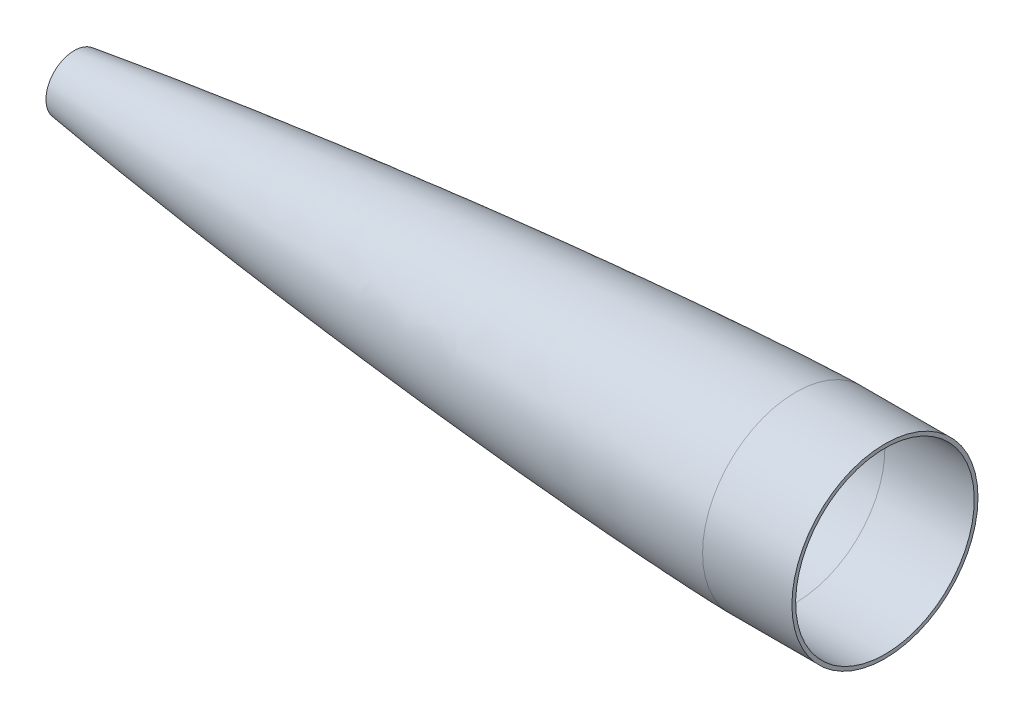
SolidWorks part; units mm, degrees
material "S-Glass Fiber"
ref_plane "Front Plane" through (0, 0, 0) normal (0, 0, 1) x (1, 0, 0)
ref_plane "Top Plane" through (0, 0, 0) normal (0, 1, 0) x (1, 0, 0)
ref_plane "Right Plane" through (0, 0, 0) normal (1, 0, 0) x (0, 0, -1)
sketch "Sketch2" plane through (0, 0, 0) normal (0, 0, 1) x (1, 0, 0)
  line L3 (762, 76.2) -> (762, 0) construction
  line L8 (762, 76.2) -> (762, 0) construction
  line L9 (146.6256, 0) -> (146.6256, 20.574) construction
  line L13 (0, 0) -> (762, 0) construction
  line L14 (0, 0) -> (2.6005, 0)
  line L15 (2.6005, 0) -> (146.6256, 20.574)
  line L16 (146.6256, 20.574) -> (146.6256, 24.13) construction
  line L18 (762, 79.375) -> (838.2, 79.375)
  line L19 (838.2, 79.375) -> (838.2, 76.2)
  line L20 (838.2, 76.2) -> (762, 76.2)
  line L21 (762, 79.375) -> (762, 76.2) construction
  spline S0 degree 4 poles (-49.3803, -13.3951) (-49.3774, -13.3872) (-49.3706, -13.3719) (-49.3515, -13.3442) (-49.3178, -13.3067) (-49.276, -13.2657) (-49.2126, -13.2108) (-49.1334, -13.1488) (-49.0162, -13.0653) (-48.8589, -12.9635) (-48.6742, -12.8535) (-48.4619, -12.7357) (-48.1531, -12.5738) (-47.6707, -12.3385) (-46.8508, -11.9725) (-45.384, -11.3821) (-42.7412, -10.4344) (-37.8908, -8.9033) (-28.7853, -6.3974) (-12.8846, -2.6091) (14.0481, 2.9702) (50.9813, 9.6302) (95.7045, 16.8265) (145.382, 24.0733) (195.1363, 30.7674) (244.9501, 37.002) (294.8122, 42.8365) (344.7156, 48.3061) (394.6553, 53.4327) (444.6281, 58.2264) (494.6316, 62.6884) (544.6644, 66.8095) (594.7257, 70.5693) (638.5543, 73.5096) (676.1401, 75.7375) (706.4525, 77.3031) (726.8599, 78.2225) (743.6263, 78.8648) (754.1247, 79.1902) (759.3746, 79.3253) (762, 79.375) knots 0 0 0 0 0 0.000041 0.000082 0.000164 0.000246 0.000328 0.000492 0.000655 0.000949 0.001243 0.001543 0.001842 0.002654 0.003867 0.005932 0.009572 0.01638 0.028732 0.052102 0.089485 0.150853 0.212221 0.27359 0.334958 0.396326 0.457695 0.519063 0.580431 0.6418 0.703168 0.764537 0.825905 0.887273 0.917957 0.948642 0.974321 0.98716 1 1 1 1 1 construction
  spline S1 degree 4 poles (0, 0) (5.3576, 1.0979) (23.0362, 4.5882) (53.13, 9.9759) (95.7045, 16.8265) (145.382, 24.0733) (195.1363, 30.7674) (244.9501, 37.002) (294.8122, 42.8365) (344.7156, 48.3061) (394.6553, 53.4327) (444.6281, 58.2264) (494.6316, 62.6884) (544.6644, 66.8095) (594.7257, 70.5693) (638.5543, 73.5096) (676.1401, 75.7375) (706.4525, 77.3031) (726.8599, 78.2225) (743.6263, 78.8648) (754.1247, 79.1902) (759.3746, 79.3253) (762, 79.375) knots 0.062743 0.062743 0.062743 0.062743 0.062743 0.089485 0.150853 0.212221 0.27359 0.334958 0.396326 0.457695 0.519063 0.580431 0.6418 0.703168 0.764537 0.825905 0.887273 0.917957 0.948642 0.974321 0.98716 1 1 1 1 1
  spline S2 degree 2 poles (146.6256, 20.574) (453.6076, 56.3921) (762, 76.2) knots 0 0 0 1 1 1
  point P1 (762, 92.8903)
  dimension "D1" = 24.13
  dimension "D2" = 146.6256
  dimension "D3" = 76.2
  dimension "D4" = 254
  dimension "D5" = 57.15
  dimension "D6" = 79.375
  dimension "32" = 762
  dimension "D7" = 20.574
  dimension "D8" = 2.6005
  dimension "D9" = 76.2
revolve "Revolve2" add sketch "Sketch2" angle 360 about L13
sketch "Sketch4" plane through (0, 0, 0) normal (1, 0, 0) x (0, 0, -1)
  circle A0 centre (0, 0) radius 24.13
  dimension "D1" = 48.26
extrude "Cut-Extrude1" cut sketch "Sketch4" along normal up to vertex (146.6256 mm away) up to point (146.6256, 0, 0)
